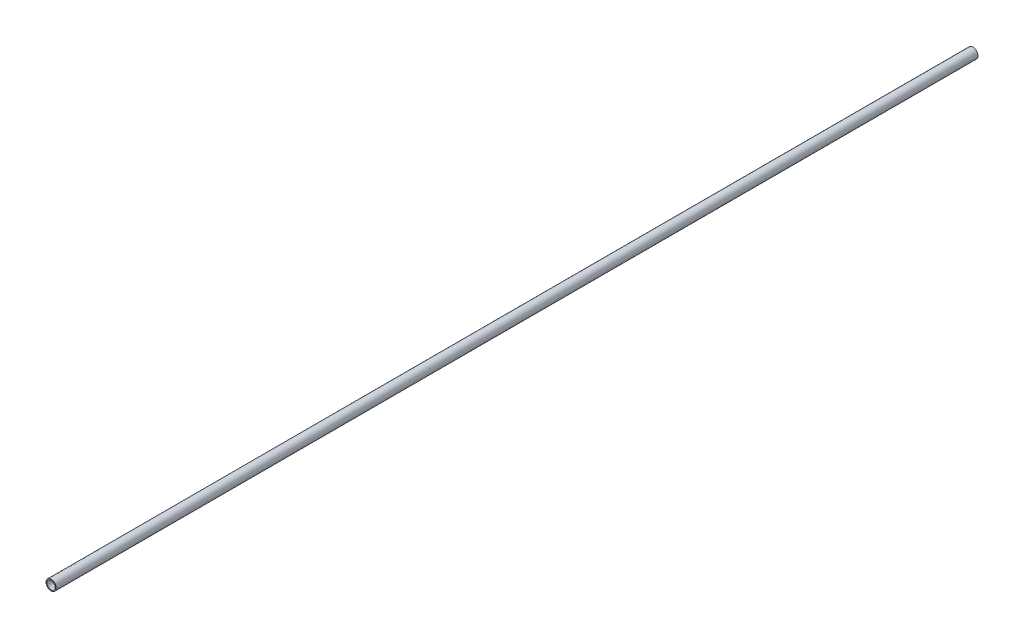
SolidWorks part; units mm, degrees
ref_plane "Front Plane" through (0, 0, 0) normal (0, 0, 1) x (1, 0, 0)
ref_plane "Top Plane" through (0, 0, 0) normal (0, 1, 0) x (1, 0, 0)
ref_plane "Right Plane" through (0, 0, 0) normal (1, 0, 0) x (0, 0, -1)
sketch "Sketch1" plane through (0, 0, 0) normal (0, 0, 1) x (1, 0, 0)
  circle A0 centre (0, 0) radius 5.5
  circle A1 centre (0, 0) radius 4.5
  dimension "D1" = 11
  dimension "D2" = 1
extrude "Boss-Extrude1" add sketch "Sketch1" along normal blind 1000
